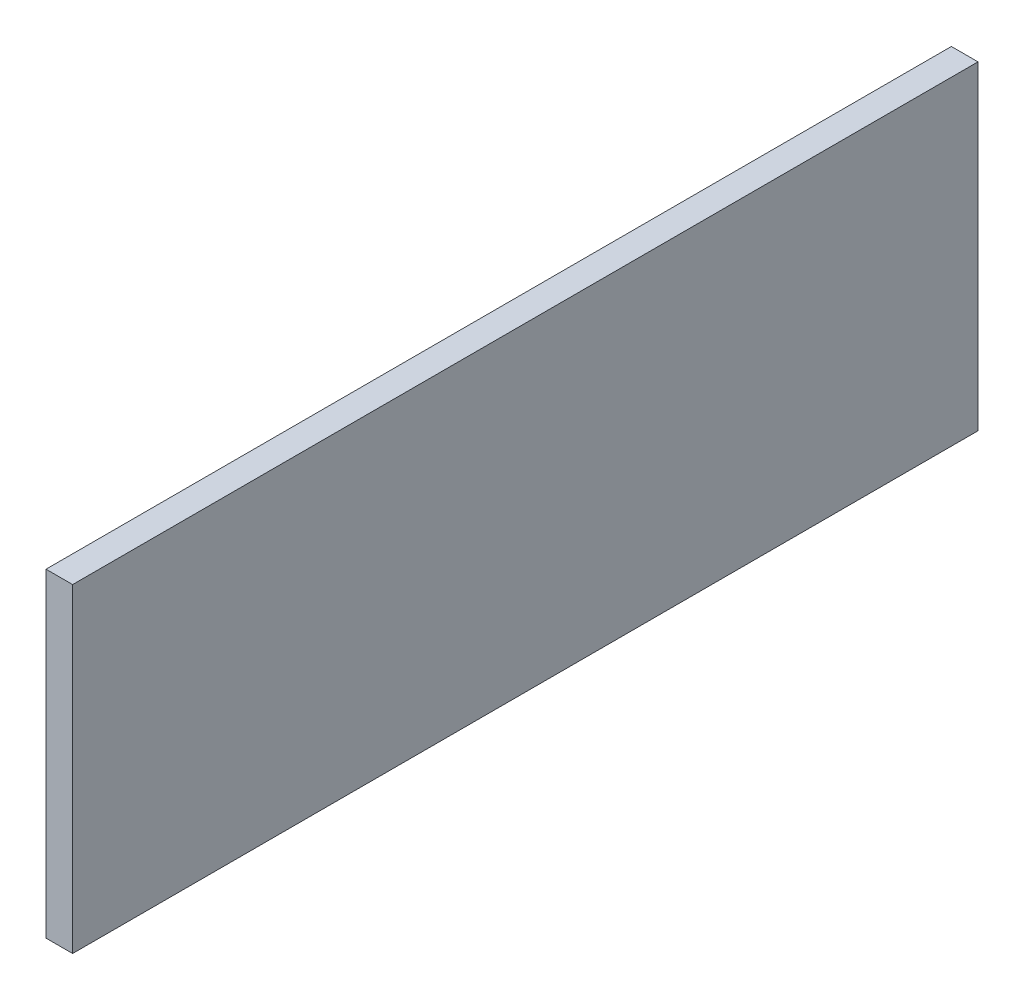
SolidWorks part; units mm, degrees
ref_plane "Front Plane" through (0, 0, 0) normal (0, 0, 1) x (1, 0, 0)
ref_plane "Top Plane" through (0, 0, 0) normal (0, 1, 0) x (1, 0, 0)
ref_plane "Right Plane" through (0, 0, 0) normal (1, 0, 0) x (0, 0, -1)
sketch "Sketch1" plane through (0, 0, 0) normal (1, 0, 0) x (0, 0, -1)
  line L1 (0, 0) -> (647.7, 0)
  line L2 (0, 0) -> (0, -228.6)
  line L3 (0, -228.6) -> (647.7, -228.6)
  line L4 (647.7, 0) -> (647.7, -228.6)
  dimension "D1" = 647.7
  dimension "D2" = 228.6
extrude "Boss-Extrude1" add sketch "Sketch1" along normal blind 19.05
